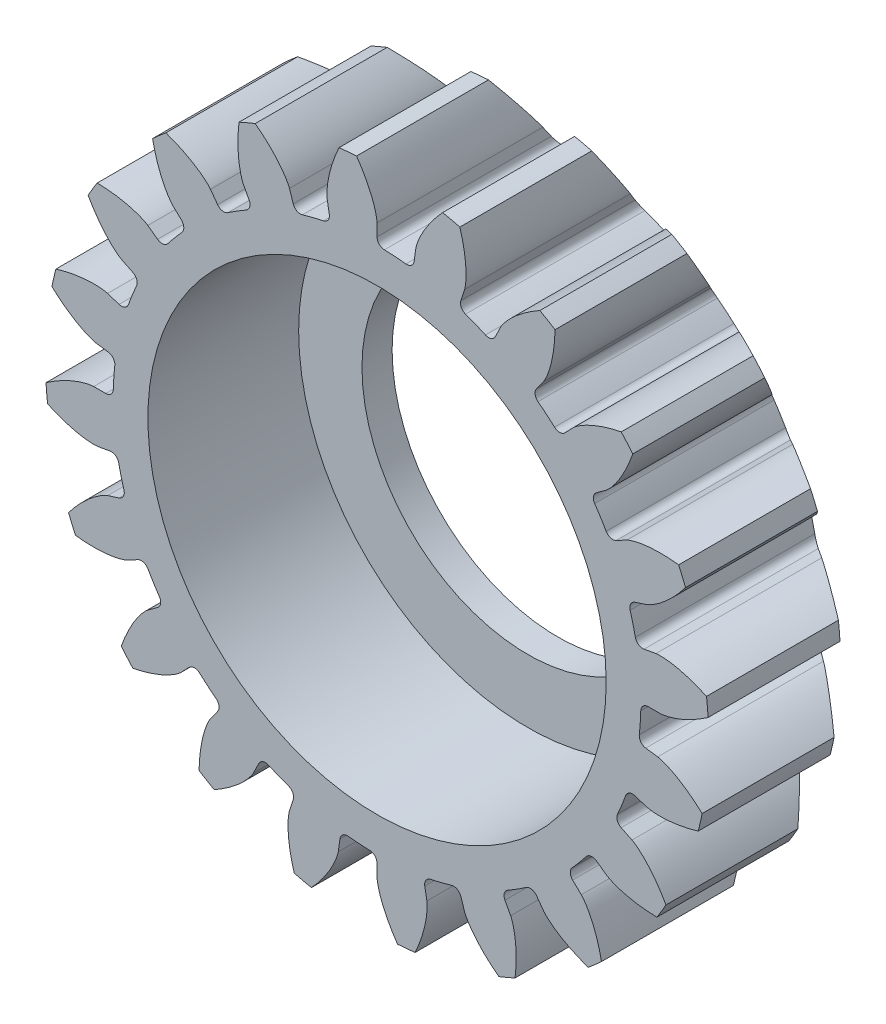
SolidWorks part; units mm, degrees
ref_plane "Front Plane" through (0, 0, 0) normal (0, 0, 1) x (1, 0, 0)
ref_plane "Top Plane" through (0, 0, 0) normal (0, 1, 0) x (1, 0, 0)
ref_plane "Right Plane" through (0, 0, 0) normal (1, 0, 0) x (0, 0, -1)
sketch "Sketch1" plane through (0, 0, 0) normal (0, 0, 1) x (1, 0, 0)
  line L0 (9.3969, 0) -> (8.75, 0)
  line L1 (10.957, 0.9716) -> (-10.957, -0.9716)
  line L2 (0, 0) -> (9.9989, 0.149) construction
  circle A0 centre (0, 0) radius 9.3969 construction
  circle A1 centre (0, 0) radius 11
  circle A2 centre (0, 0) radius 8.75
  circle A3 centre (0, 0) radius 10 construction
  spline S0 degree 4 poles (9.3969, 0) (9.4039, 0.0001) (9.4233, 0.001) (9.4601, 0.0044) (9.5198, 0.0126) (9.5953, 0.0267) (9.6923, 0.0492) (9.8055, 0.0811) (9.9285, 0.1217) (10.0606, 0.172) (10.1907, 0.2274) (10.3189, 0.2874) (10.4449, 0.3516) (10.5954, 0.4343) (10.7729, 0.5404) (10.9755, 0.6744) (11.1993, 0.8377) (11.4205, 1.016) (11.6321, 1.2011) (11.8386, 1.3988) (12.0332, 1.5975) (12.2272, 1.8143) (12.4021, 2.0197) (12.5886, 2.2606) (12.7364, 2.4583) (12.9206, 2.73) (13.0263, 2.8938) (13.1461, 3.089) (13.1973, 3.1776) (13.2289, 3.2321) knots 0 0 0 0 0 0.005377 0.015084 0.028532 0.04661 0.064855 0.092111 0.119476 0.146842 0.174209 0.201575 0.228941 0.256307 0.307035 0.361767 0.4165 0.471232 0.525964 0.580697 0.635429 0.690161 0.744894 0.799626 0.854358 0.909091 0.954545 1 1 1 1 1 construction
  spline S1 degree 4 poles (9.3969, 0) (9.4039, 0.0001) (9.4233, 0.001) (9.4601, 0.0044) (9.5198, 0.0126) (9.5953, 0.0267) (9.6923, 0.0492) (9.8055, 0.0811) (9.9285, 0.1217) (10.0606, 0.172) (10.1907, 0.2274) (10.3189, 0.2874) (10.4449, 0.3516) (10.5954, 0.4343) (10.7729, 0.5404) (10.9755, 0.6744) (11.1993, 0.8377) (11.4205, 1.016) (11.6321, 1.2011) (11.8386, 1.3988) (12.0332, 1.5975) (12.2272, 1.8143) (12.4021, 2.0197) (12.5886, 2.2606) (12.7364, 2.4583) (12.8807, 2.6711) (12.9497, 2.776) (12.9844, 2.8301) knots 0 0 0 0 0 0.005377 0.015084 0.028532 0.04661 0.064855 0.092111 0.119476 0.146842 0.174209 0.201575 0.228941 0.256307 0.307035 0.361767 0.4165 0.471232 0.525964 0.580697 0.635429 0.690161 0.744894 0.799626 0.854358 0.909091 0.909091 0.909091 0.909091 0.909091
  dimension "D1" = 18.7939
  dimension "D2" = 22
  dimension "D3" = 17.5
  dimension "D5" = 20
  dimension "D4" = 4.214
extrude "Boss-Extrude3" add sketch "Sketch1" along normal blind 6 contours L1 A2 | A2 L1 | L0 S1 A1 L1 A2
mirror "Mirror2" about plane through (0, 0, 6) normal (0.0883, -0.9961, 0) of "Boss-Extrude3"
fillet "Fillet1" radius 0.25 2 edges at (8.6135, 1.5397, 3) (8.75, 0, 3)
pattern_circular "CirPattern8" count 20 over 360 about axis through (0, 0, 6) along (0, 0, -1) of "Boss-Extrude3", "Mirror2", "Fillet1"
sketch "Sketch3" plane through (0, 0, 6) normal (0, 0, 1) x (1, 0, 0)
  circle A0 centre (0, 0) radius 7.6
  dimension "D1" = 15.2
extrude "Cut-Extrude2" cut sketch "Sketch3" against normal through all
sketch "Sketch4" plane through (0, 0, 0) normal (0, 0, -1) x (-1, 0, 0)
  circle A0 centre (0, 0) radius 3
  circle A2 centre (0, 0) radius 1.5
  dimension "D1" = 6
extrude "Boss-Extrude4" [suppressed] add sketch "Sketch4" along normal blind 1
sketch "Sketch5" plane through (0, 0, 0) normal (0, 1, 0) x (1, 0, 0)
  line L0 (0, 0) -> (11.0362, 0)
  line L1 (11.0362, 0) -> (11.0362, -1.65)
  line L2 (11.0362, -1.65) -> (8.6798, 0)
  line L3 (0, 0) -> (0, 4.7475) construction
  dimension "D1" = 55
  dimension "D2" = 1.65
revolve "Cut-Revolve1" cut sketch "Sketch5" angle 360 about L3
sketch "Sketch6" plane through (0, 0, 0) normal (0, 0, -1) x (-1, 0, 0)
  circle A0 centre (0, 0) radius 7.6
  circle A1 centre (0, 0) radius 5.5
  dimension "D1" = 11
extrude "Boss-Extrude5" add sketch "Sketch6" against normal blind 1
equation "\"d\"= 20'Pitch diameter"
equation "\"N\"= 20'Number of teeth"
equation "\"bl\"= 0.1mm'Backlash"
equation "\"pa\"= 20deg'Pressure angle (deg)"
equation "\"pc\"= ( 3.1415 * \"d\" ) / \"N\"\t'Circular pitch"
equation "\"m\"= \"d\" / \"N\"\t\t\t'module"
equation "\"P\"= \"N\" / \"d\"\t\t\t'Diametral pitch"
equation "\"a\"= 1/\"P\"\t\t\t'Addendum distance"
equation "\"b\"= 1.25 / \"P\"'Dedendum distance"
equation "\"rb\"= (\"d\"/2)*cos(\"pa\")\t\t'base circle radius"
equation "\"cp\"= 3.1415/\"P\"\t\t'Circular pitch"
equation "\"t\"= ( \"cp\" / 2 ) - \"bl\"'tooth tickness"
equation "\"c\"=\"b\"-\"a\"\t\t\t'Clearance"
equation "\"facewidth\"= 6'face width"
equation "\"rbd\"= \"rb\" * 2'base circle diameter"
equation "\"D1@Sketch1\"=\"rbd\""
equation "\"D2@Sketch1\"= \"d\" + (\"a\" * 2)"
equation "\"D3@Sketch1\" = \"ded\""
equation "\"D4@Sketch1\"= ((\"t\" /2) / (\"d\"/2)) * (180/3.1415)"
equation "\"D1@Boss-Extrude3\"=\"facewidth\""
equation "\"D1@Fillet1\"=\"c\""
equation "\"D1@CirPattern8\"=\"N\""
equation "\"D5@Sketch1\"=\"d\""
equation "\"ded1\"= \"d\" - 2 * ( ( ( \"d\" / 2 ) - \"rb\" ) + ( 0.5 * ( 1.25 / \"P\" ) ) )"
equation "\"ded2\"= \"d\" - ( \"b\" * 2 )"
equation "\"ded\"= IIF ( \"rb\" < ( \"ded2\" / 2 ) , \"ded1\" , \"ded2\" )"
equation "\"shaftdia\"= 15.2"
equation "\"D1@Sketch3\"=\"shaftdia\""
